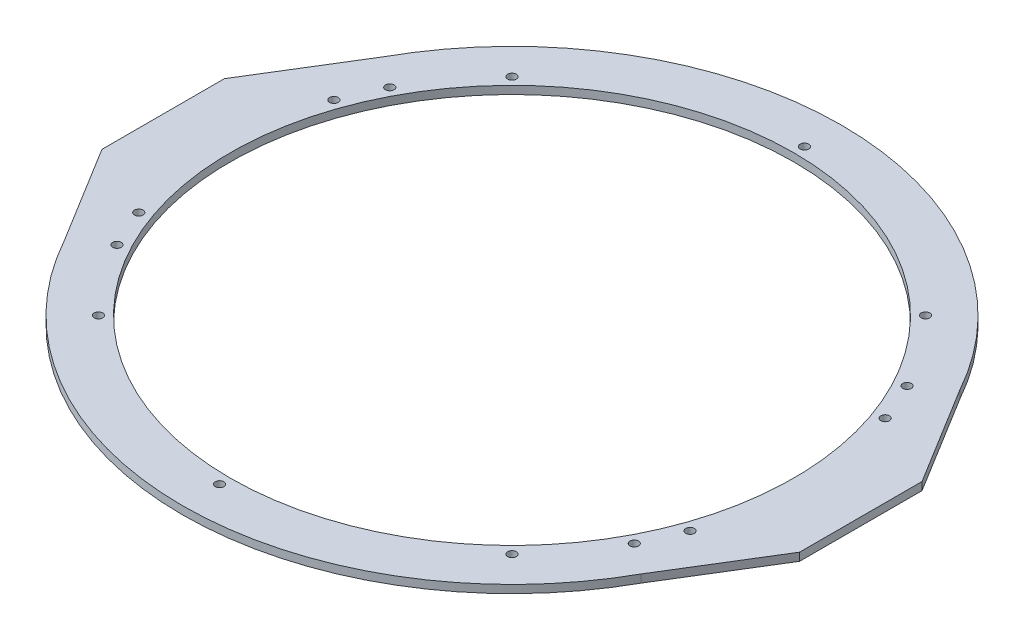
SolidWorks part; units mm, degrees
ref_plane "Front Plane" through (0, 0, 0) normal (0, 0, 1) x (1, 0, 0)
ref_plane "Top Plane" through (0, 0, 0) normal (0, 1, 0) x (1, 0, 0)
ref_plane "Right Plane" through (0, 0, 0) normal (1, 0, 0) x (0, 0, -1)
sketch "Sketch1" plane through (0, 0, 0) normal (0, 1, 0) x (1, 0, 0)
  line L0 (337.3, 0) -> (394.45, 0) construction
  circle A0 centre (0, 0) radius 394.45
  circle A1 centre (0, 0) radius 337.3
  circle A2 centre (0, 0) radius 350 construction
  circle A3 centre (0, 0) radius 350 construction
  dimension "D1" = 44.45
  dimension "D2" = 12.7
extrude "Boss-Extrude1" add sketch "Sketch1" along normal blind 9.525
sketch "Sketch2" plane through (0, 9.525, 0) normal (0, 1, 0) x (1, 0, 0)
  line L0 (0, 0) -> (0, 76.2) construction
  line L1 (0, 0) -> (-213.7892, 0) construction
  line L9 (-380.73, 103.1284) -> (-444.23, 103.1284)
  line L10 (-380.73, 103.1284) -> (-380.73, -103.1284)
  line L11 (-380.73, -103.1284) -> (-444.23, -103.1284)
  line L12 (-444.23, 103.1284) -> (-444.23, -103.1284)
  circle A0 centre (0, 0) radius 394.45 construction
  dimension "D1" = 63.5
extrude "Cut-Extrude1" cut sketch "Sketch2" against normal through all
sketch "Sketch5" plane through (0, 0, 0) normal (0, 1, 0) x (1, 0, 0)
  line L2 (278.0649, 190.922) -> (417.5487, 190.922)
  line L3 (417.5487, 190.922) -> (417.5487, -190.922)
  line L4 (417.5487, -190.922) -> (278.0649, -190.922)
  circle A0 centre (0, 0) radius 337.3 construction
  arc A1 (278.0649, -190.922) -> (278.0649, 190.922) centre (0, 0) ccw
  arc A2 (278.0649, 190.922) -> (278.0649, -190.922) centre (0, 0) ccw construction
extrude "Boss-Extrude4" add sketch "Sketch5" along normal up to surface (9.525 mm away) up to face at (6.86, 9.525, 0)
mirror "Mirror1" about plane through (0, 0, 0) normal (1, 0, 0) of "Boss-Extrude4"
hole_wizard "3/8 Clearance Hole1" positions "Sketch7" profile "Sketch8" hole size "3/8" standard "ANSI Inch" end condition through all
sketch "Sketch7" plane through (0, 9.525, 0) normal (0, 1, 0) x (-1, 0, 0)
  circle A2 centre (0, 0) radius 350 construction
  point P0 (-329.9557, 116.7442)
  point P2 (-309.5803, 163.2789)
  dimension "D1" = 50.8
sketch "Sketch8" plane through (329.9557, 9.525, 116.7442) normal (1, 0, 0) x (0, 0, 1)
  line L0 (0, 0) -> (0, 9.525)
  line L1 (0, 9.525) -> (5.1587, 9.525)
  line L2 (5.1587, 9.525) -> (5.1587, 0)
  line L5 (5.1587, 0) -> (0, 0)
  line L11 (0, -6.35) -> (0, 107.95) construction
  dimension "Thru Hole Dia." = 10.3175
  dimension "Thru Hole Depth" = 9.525
mirror "Mirror2" about plane through (0, 0, 0) normal (1, 0, 0) of "3/8 Clearance Hole1"
mirror "Mirror3" about plane through (0, 0, 0) normal (0, 0, 1) of "Mirror2", "3/8 Clearance Hole1"
hole_wizard "3/8 Clearance Hole2" positions "Sketch10" profile "Sketch11" hole size "3/8" standard "ANSI Inch" end condition through all
sketch "Sketch10" plane through (0, 9.525, 0) normal (0, 1, 0) x (1, 0, 0)
  circle A0 centre (0, 0) radius 350 construction
  point P0 (247.4874, -247.4874)
sketch "Sketch11" plane through (247.4874, 9.525, 247.4874) normal (1, 0, 0) x (0, 0, 1)
  line L0 (0, 0) -> (0, 9.525)
  line L1 (0, 9.525) -> (5.1587, 9.525)
  line L2 (5.1587, 9.525) -> (5.1587, 0)
  line L5 (5.1587, 0) -> (0, 0)
  line L11 (0, -6.35) -> (0, 107.95) construction
  dimension "Thru Hole Dia." = 10.3175
  dimension "Thru Hole Depth" = 9.525
pattern_circular "CirPattern1" count 8 over 360 skipping 1, 5 of "3/8 Clearance Hole2"
ref_plane "Plane1" through (350, 0, 0) normal (1, 0, 0) x (0, 0, -1)
sketch "Sketch12" plane through (0, 0, 0) normal (0, 1, 0) x (1, 0, 0)
  line L1 (-417.5487, 190.922) -> (-345.1661, 190.922) construction
  line L2 (-417.5487, 190.922) -> (-417.5487, 73.2544)
  line L3 (-417.5487, 190.922) -> (-345.1661, 190.922)
  line L4 (-345.1661, 190.922) -> (-417.5487, 73.2544)
  line L5 (-417.5487, -190.922) -> (-417.5487, 190.922) construction
extrude "Cut-Extrude5" cut sketch "Sketch12" along normal through all
mirror "Mirror8" about plane through (0, 0, 0) normal (0, 0, 1) of "Cut-Extrude5"
mirror "Mirror9" about plane through (0, 0, 0) normal (1, 0, 0) of "Mirror8", "Cut-Extrude5"
